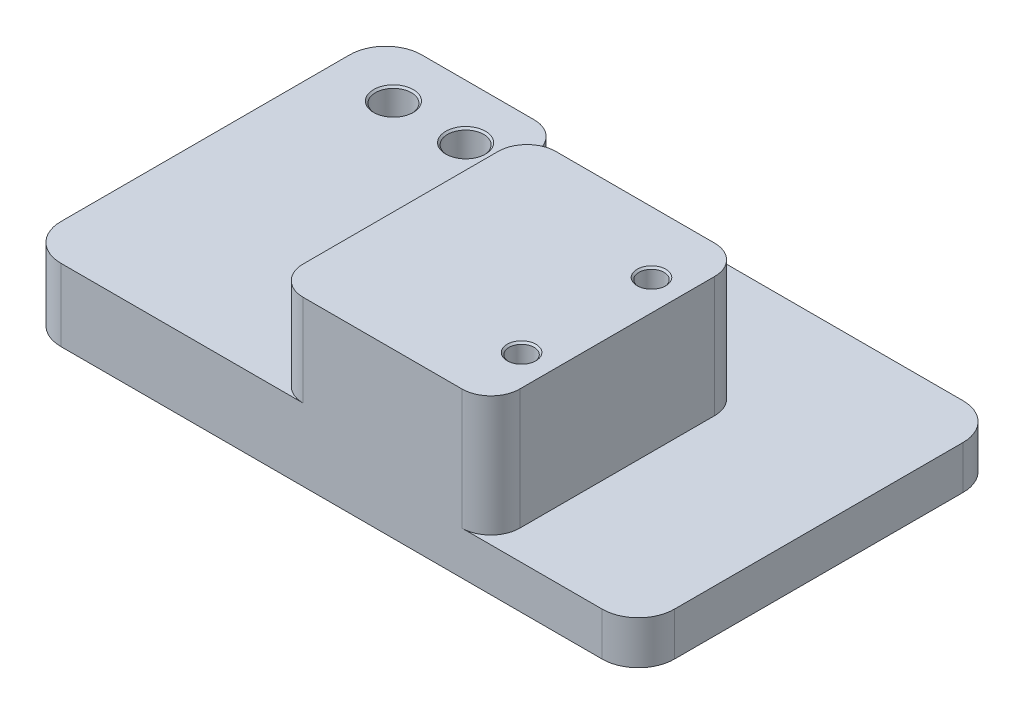
SolidWorks part; units mm, degrees
ref_plane "Front Plane" through (0, 0, 0) normal (0, 0, 1) x (1, 0, 0)
ref_plane "Top Plane" through (0, 0, 0) normal (0, 1, 0) x (1, 0, 0)
ref_plane "Right Plane" through (0, 0, 0) normal (1, 0, 0) x (0, 0, -1)
sketch "Sketch1" plane through (0, 0, 0) normal (0, 1, 0) x (1, 0, 0)
  line L1 (0, 0) -> (85, 0)
  line L2 (0, 0) -> (0, 50)
  line L3 (0, 50) -> (85, 50)
  line L4 (85, 0) -> (85, 50)
extrude "Boss-Extrude1" add sketch "Sketch1" along normal blind 6
sketch "Sketch2" plane through (0, 6, 0) normal (0, 1, 0) x (1, 0, 0)
  line L1 (85, 50) -> (0, 50) construction
  line L5 (0, 0) -> (85, 0) construction
  line L8 (0, 0) -> (0, 50)
  line L9 (0, 50) -> (24.5743, 50)
  line L10 (24.5743, 50) -> (24.5743, 35)
  line L11 (24.5743, 35) -> (9.5743, 35)
  line L12 (9.5743, 35) -> (9.5743, 0)
  line L13 (9.5743, 0) -> (0, 0)
extrude "Boss-Extrude2" add sketch "Sketch2" along normal blind 4
sketch "Sketch4" plane through (0, 10, 0) normal (0, 1, 0) x (1, 0, 0)
  line L0 (24.5743, 42.5) -> (18.5743, 42.5) construction
  line L1 (24.5743, 35) -> (24.5743, 50) construction
  line L2 (18.5743, 42.5) -> (8.5743, 42.5) construction
  circle A0 centre (18.5743, 42.5) radius 2.5
  circle A1 centre (8.5743, 42.5) radius 2.5
  dimension "D1" = 10
extrude "Cut-Extrude2" cut sketch "Sketch4" against normal blind 11
sketch "Sketch5" plane through (0, 6, 0) normal (0, 1, 0) x (1, 0, 0)
  line L1 (9.5743, 35) -> (9.5743, 0)
  line L5 (9.5743, 0) -> (64.5743, 0)
  line L6 (9.5743, 0) -> (85, 0) construction
  line L7 (64.5743, 0) -> (64.5743, 35)
  line L8 (64.5743, 35) -> (9.5743, 35)
extrude "Boss-Extrude3" add sketch "Sketch5" along normal blind 16.7
fillet "Fillet1" radius 5 4 edges at (85, 3, -50) (85, 3, 0) (0, 5, -50) (0, 5, 0)
sketch "Sketch6" plane through (0, 22.7, 0) normal (0, 1, 0) x (1, 0, 0)
  line L0 (64.5743, 17.5) -> (60.3243, 17.5) construction
  line L1 (64.5743, 0) -> (64.5743, 35) construction
  line L2 (60.3243, 17.5) -> (60.3243, 26.5) construction
  circle A0 centre (60.3243, 26.5) radius 1.74
  circle A1 centre (60.3243, 8.5) radius 1.74
extrude "Cut-Extrude3" cut sketch "Sketch6" against normal blind 10
sketch "Sketch7" plane through (0, 22.7, 0) normal (0, 1, 0) x (1, 0, 0)
  line L0 (9.5743, 35) -> (34.5743, 35)
  line L1 (64.5743, 35) -> (9.5743, 35) construction
  line L2 (34.5743, 35) -> (34.5743, 0)
  line L3 (9.5743, 0) -> (64.5743, 0) construction
  line L4 (34.5743, 0) -> (9.5743, 0)
  line L5 (9.5743, 0) -> (9.5743, 35)
extrude "Cut-Extrude4" cut sketch "Sketch7" against normal up to surface (12.7 mm away) up to face at (18.5743, 10, -40)
fillet "Fillet3" radius 4 4 edges at (64.5743, 14.35, 0) (64.5743, 14.35, -35) (34.5743, 16.35, -35) (34.5743, 16.35, 0)
fillet "Fillet4" radius 4 1 edges at (24.5743, 8, -35)
fillet "Fillet5" radius 4 1 edges at (24.5743, 8, -50)
chamfer "Chamfer1" distance 0.25 angle 45 4 edges at (60.3243, 22.7, -10.24) (60.3243, 22.7, -24.76) (8.5743, 10, -40) (18.5743, 10, -40)
